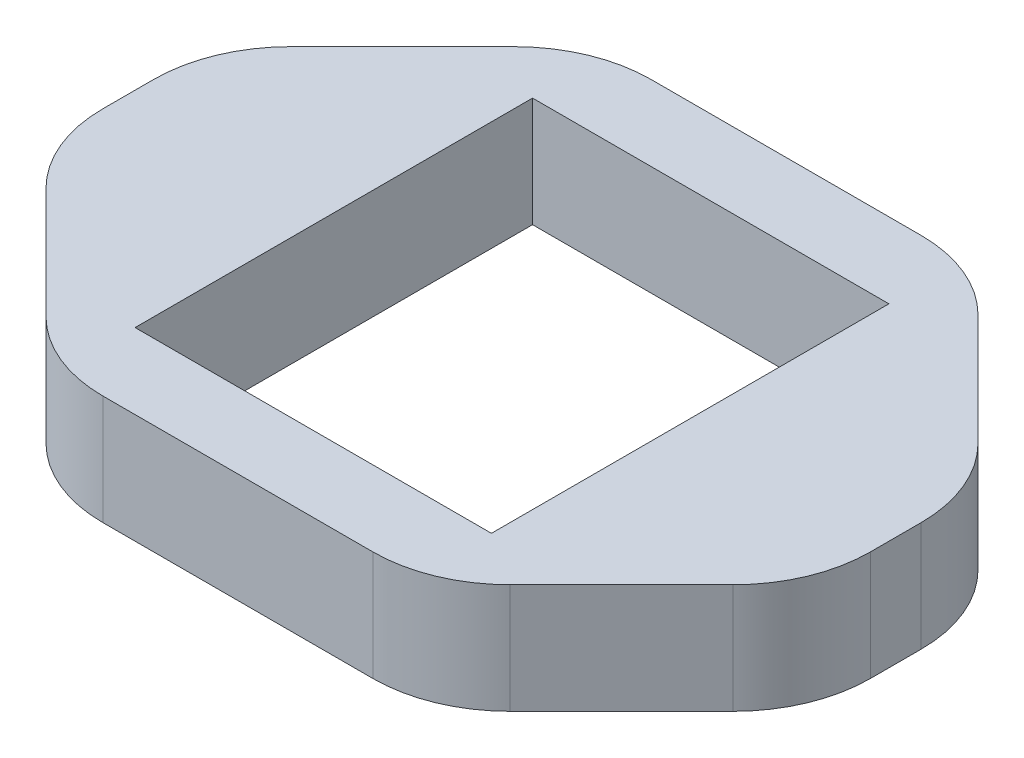
SolidWorks part; units mm, degrees
ref_plane "Plan de face" through (0, 0, 0) normal (0, 0, 1) x (1, 0, 0)
ref_plane "Plan de dessus" through (0, 0, 0) normal (0, 1, 0) x (1, 0, 0)
ref_plane "Plan de droite" through (0, 0, 0) normal (1, 0, 0) x (0, 0, -1)
sketch "Esquisse1" plane through (0, 0, 0) normal (0, 1, 0) x (1, 0, 0)
  line L5 (-14, -10) -> (14, -10)
  line L6 (-14, -10) -> (-14, 10)
  line L7 (-14, 10) -> (14, 10)
  line L8 (14, -10) -> (14, 10)
  line L9 (-14, -10) -> (14, 10) construction
  line L10 (-14, 10) -> (14, -10) construction
  point P0 (0, 0)
  dimension "D1" = 28
  dimension "D2" = 20
extrude "Boss.-Extru.1" add sketch "Esquisse1" along normal blind 4
sketch "Esquisse2" plane through (0, 4, 0) normal (0, 1, 0) x (1, 0, 0)
  line L1 (-6.5, -7.25) -> (6.5, -7.25)
  line L2 (-6.5, -7.25) -> (-6.5, 7.25)
  line L3 (-6.5, 7.25) -> (6.5, 7.25)
  line L4 (6.5, -7.25) -> (6.5, 7.25)
  line L5 (-6.5, -7.25) -> (6.5, 7.25) construction
  line L6 (-6.5, 7.25) -> (6.5, -7.25) construction
  point P0 (0, 0)
  dimension "D1" = 14.5
  dimension "D2" = 13
extrude "Enlèv. mat.-Extru.1" cut sketch "Esquisse2" against normal blind 4
sketch "Esquisse3" plane through (0, 4, 0) normal (0, 1, 0) x (1, 0, 0)
  line L0 (-14, 3) -> (-7, 10)
  line L1 (-14, -3) -> (-7, -10)
  line L2 (7, -10) -> (14, -3)
  line L3 (14, 3) -> (7, 10)
  line L4 (14, -10) -> (14, 10)
  line L5 (14, 10) -> (-14, 10)
  line L6 (-14, 10) -> (-14, -10)
  line L7 (-14, -10) -> (14, -10)
  line L8 (14, -10) -> (14, 10)
  line L9 (14, 10) -> (-14, 10)
  line L10 (-14, 10) -> (-14, -10)
  line L11 (-14, -10) -> (14, -10)
  line M9 (14, -10) -> (14, 10)
  line M10 (14, 10) -> (-14, 10)
  line M11 (-14, 10) -> (-14, -10)
  line M12 (-14, -10) -> (14, -10)
  dimension "D2" = 7
  dimension "D3" = 7
  dimension "D4" = 7
  dimension "D5" = 7
  dimension "D6" = 7
  dimension "D7" = 7
  dimension "D8" = 7
  dimension "D9" = 7
  dimension "D1" = 0
extrude "Enlèv. mat.-Extru.2" cut sketch "Esquisse3" against normal blind 4 contours L0 M11 M10 | L3 M9 M10 | L2 M12 M9 | L1 M11 M12
fillet "Congé2" radius 5 8 edges at (14, 2, -3) (7, 2, -10) (-7, 2, -10) (-14, 2, -3) (14, 2, 3) (7, 2, 10) (-7, 2, 10) (-14, 2, 3)
